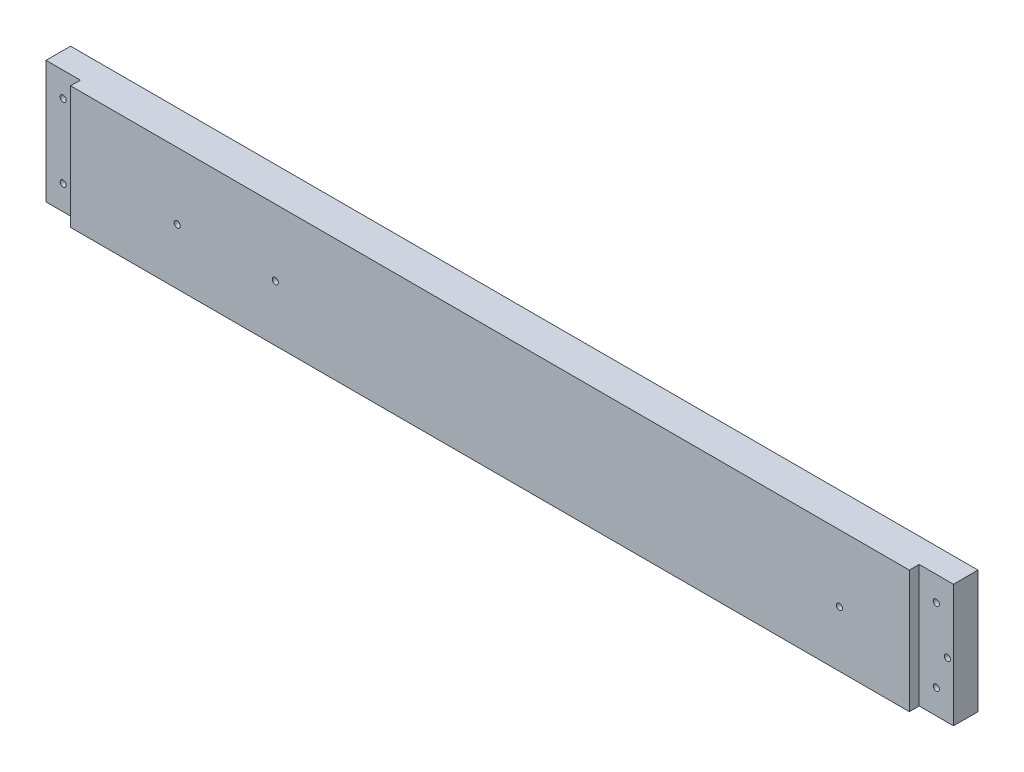
SolidWorks part; units mm, degrees
material "Pine"
ref_plane "Front Plane" through (0, 0, 0) normal (0, 0, 1) x (1, 0, 0)
ref_plane "Top Plane" through (0, 0, 0) normal (0, 1, 0) x (1, 0, 0)
ref_plane "Right Plane" through (0, 0, 0) normal (1, 0, 0) x (0, 0, -1)
sketch "Sketch1" plane through (0, 0, 0) normal (0, 0, 1) x (1, 0, 0)
  line L0 (8932.6508, -5243.5125) -> (10226.1458, -5243.5125)
  line L1 (9086.3208, -4722.0918) -> (10222.9708, -4853.7812)
  line L2 (8914.8708, -6342.0625) -> (10197.5708, -6342.0625)
  line L3 (8914.8708, -5808.6625) -> (10197.5708, -5808.6625)
  line L4 (8919.6333, -5253.0375) -> (10218.2083, -5253.0375)
  line L5 (9134.2633, -4656.1375) -> (9134.2633, -4638.3575)
  line L6 (9091.0833, -4638.3575) -> (9134.2633, -4638.3575)
  line L7 (9091.0833, -4567.2375) -> (9091.0833, -4638.3575)
  line L8 (9134.2633, -4656.1375) -> (9581.3033, -4656.1375)
  line L9 (9091.0833, -4567.2375) -> (9624.4833, -4567.2375)
  line L10 (9581.3033, -4656.1375) -> (9581.3033, -4638.3575)
  line L11 (9581.3033, -4638.3575) -> (9624.4833, -4638.3575)
  line L12 (9624.4833, -4567.2375) -> (9624.4833, -4638.3575)
  line L13 (8932.6508, -5225.7325) -> (9344.9775, -5225.7325)
  line L14 (8932.6508, -5256.2125) -> (8932.6508, -5243.5125)
  line L15 (8911.6958, -5256.2125) -> (8932.6508, -5256.2125)
  line L16 (8914.8708, -4722.0918) -> (9086.3208, -4722.0918)
  line L17 (8911.6958, -4715.5913) -> (8932.6508, -4715.5913)
  line L18 (8914.8708, -6342.0625) -> (8914.8708, -5808.6625)
  line L19 (12082.9917, -4722.0918) -> (10946.3417, -4853.7812)
  line L20 (12236.6617, -5243.5125) -> (10943.1667, -5243.5125)
  line L21 (10951.1042, -5253.0375) -> (12249.6792, -5253.0375)
  line L22 (10838.3917, -5656.2625) -> (11308.2917, -5656.2625)
  line L23 (10838.3917, -5719.7625) -> (11308.2917, -5719.7625)
  line L24 (10838.3917, -5742.5368) -> (11308.2917, -5742.5368)
  line L25 (10806.6417, -6342.0625) -> (11340.0417, -6342.0625)
  line L26 (10803.4667, -6335.7125) -> (11343.2167, -6335.7125)
  line L27 (10803.4667, -6317.9325) -> (11343.2167, -6317.9325)
  line L28 (10943.1667, -5225.7325) -> (11376.4483, -5225.7325)
  line L29 (11506.7292, -4754.5625) -> (10806.6417, -4827.5875)
  line L30 (11506.7292, -4567.2375) -> (11506.7292, -4754.5625)
  line L31 (10806.6417, -4567.2375) -> (10806.6417, -4827.5875)
  line L32 (10806.6417, -4567.2375) -> (11506.7292, -4567.2375)
  line L33 (10235.6708, -6329.3625) -> (10245.1958, -6329.3625)
  line L34 (10245.1958, -6329.3625) -> (10254.7208, -6278.5625)
  line L35 (10302.3458, -6329.3625) -> (10311.8708, -6278.5625)
  line L36 (10302.3458, -6329.3625) -> (10292.8208, -6329.3625)
  line L37 (10245.1958, -5821.3625) -> (10254.7208, -5872.1625)
  line L38 (10235.6708, -5821.3625) -> (10245.1958, -5821.3625)
  line L39 (10292.8208, -5821.3625) -> (10302.3458, -5821.3625)
  line L40 (10302.3458, -5821.3625) -> (10311.8708, -5872.1625)
  line L41 (10235.6708, -5821.3625) -> (10235.6708, -6329.3625)
  line L42 (10254.7208, -5872.1625) -> (10254.7208, -6278.5625)
  line L43 (10311.8708, -5872.1625) -> (10311.8708, -6278.5625)
  line L44 (10292.8208, -5821.3625) -> (10292.8208, -6329.3625)
  line L45 (8932.6508, -5225.7325) -> (8932.6508, -4715.5913)
  line L46 (8911.6958, -4715.5913) -> (8911.6958, -5256.2125)
  line L47 (8914.8708, -5248.275) -> (8914.8708, -4722.0918)
  line L48 (8919.6333, -5253.0375) -> (8914.8708, -5248.275)
  line L49 (8914.8708, -5145.0875) -> (8937.426, -5145.0875)
  line L50 (8914.8708, -5202.2375) -> (8937.426, -5202.2375)
  line L51 (10838.3917, -5656.2625) -> (10838.3917, -5719.7625)
  line L52 (10832.0417, -5736.1868) -> (10856.1717, -5736.1868)
  line L53 (10806.6417, -6342.0625) -> (10806.6417, -5818.7368)
  line L54 (10832.0417, -5649.9125) -> (10856.1717, -5649.9125)
  line L55 (10832.0417, -5726.1125) -> (10856.1717, -5726.1125)
  line L56 (10806.6417, -5818.7368) -> (10833.9015, -5818.7368)
  line L57 (10832.0417, -5806.0442) -> (10851.6815, -5806.0442)
  line L58 (10856.1717, -5801.5541) -> (10856.1717, -5736.1868)
  line L59 (10838.3917, -5814.2467) -> (10838.3917, -5742.5368)
  line L60 (10832.0417, -5806.0442) -> (10832.0417, -5736.1868)
  line L61 (10803.4667, -6317.9325) -> (10803.4667, -6335.7125)
  line L62 (10197.5708, -5808.6625) -> (10197.5708, -6342.0625)
  line L63 (9762.3842, -6348.4125) -> (9762.3842, -5802.3125)
  line L64 (9780.1642, -6348.4125) -> (9762.3842, -6348.4125)
  line L65 (9780.1642, -5802.3125) -> (9780.1642, -6348.4125)
  line L66 (9762.3842, -5802.3125) -> (9780.1642, -5802.3125)
  line L67 (9332.2775, -6348.4125) -> (9332.2775, -5802.3125)
  line L68 (9332.2775, -6348.4125) -> (9350.0575, -6348.4125)
  line L69 (9350.0575, -5802.3125) -> (9350.0575, -6348.4125)
  line L70 (9332.2775, -5802.3125) -> (9350.0575, -5802.3125)
  line L71 (9993.8374, -6061.075) -> (9993.8374, -6045.2418)
  line L72 (9998.5999, -6065.8375) -> (10014.4331, -6065.8375)
  line L73 (9998.5999, -6084.8875) -> (10014.4331, -6084.8875)
  line L74 (9993.8374, -6105.4832) -> (9993.8374, -6089.65)
  line L75 (9974.7874, -6105.4832) -> (9974.7874, -6089.65)
  line L76 (9954.1917, -6084.8875) -> (9970.0249, -6084.8875)
  line L77 (9974.7874, -6061.075) -> (9974.7874, -6045.2418)
  line L78 (9954.1917, -6065.8375) -> (9970.0249, -6065.8375)
  line L79 (10793.9417, -6237.2875) -> (10816.4969, -6237.2875)
  line L80 (10793.9417, -6294.4375) -> (10816.4969, -6294.4375)
  line L81 (10856.1717, -5649.9125) -> (10856.1717, -5726.1125)
  line L82 (10832.0417, -5726.1125) -> (10832.0417, -5649.9125)
  line L83 (10226.1458, -5225.7325) -> (10226.1458, -5243.5125)
  line L84 (10205.1908, -5257.8) -> (10205.1908, -4844.2499)
  line L85 (10230.9083, -4844.2499) -> (10230.9083, -5257.8)
  line L86 (10205.1908, -5257.8) -> (10230.9083, -5257.8)
  line L87 (10205.1908, -4844.2499) -> (10230.9083, -4844.2499)
  line L88 (10946.3417, -5176.8375) -> (10968.8969, -5176.8375)
  line L89 (9349.4676, -5141.9125) -> (9358.2674, -5141.9125)
  line L90 (10946.3417, -5119.6875) -> (10968.8969, -5119.6875)
  line L91 (9929.011, -4660.9635) -> (10066.0807, -4660.9635)
  line L92 (9929.011, -4678.7435) -> (10066.0807, -4678.7435)
  line L93 (10943.1667, -5225.7325) -> (10943.1667, -5243.5125)
  line L94 (10946.3417, -5248.275) -> (10951.1042, -5253.0375)
  line L95 (10946.3417, -5257.8063) -> (10946.3417, -4849.0188)
  line L96 (10964.1217, -5257.8) -> (10964.1217, -4844.2499)
  line L97 (10938.4042, -4844.2499) -> (10938.4042, -5257.8)
  line L98 (10938.4042, -5257.8) -> (10964.1217, -5257.8)
  line L99 (10964.1217, -4844.2499) -> (10938.4042, -4844.2499)
  line L100 (10344.8908, -4560.8875) -> (10369.0208, -4560.8875)
  line L101 (10344.8908, -4560.8875) -> (10369.0208, -4560.8875)
  line L102 (10800.2917, -4560.8875) -> (10824.4217, -4560.8875)
  line L103 (10200.4156, -5119.6875) -> (10222.9708, -5119.6875)
  line L104 (10200.4156, -5176.8375) -> (10222.9708, -5176.8375)
  line L105 (9344.9775, -5146.4026) -> (9344.9775, -5225.7325)
  line L106 (10344.8908, -4560.8875) -> (10344.8908, -4833.9375)
  line L107 (9792.8642, -5225.7325) -> (9792.8642, -5146.4026)
  line L108 (9362.7575, -5225.7325) -> (9775.0842, -5225.7325)
  line L109 (9680.3633, -4761.8396) -> (9680.3633, -4559.9604)
  line L110 (9656.2333, -4559.9604) -> (9680.3633, -4559.9604)
  line L111 (9656.2333, -4761.8396) -> (9680.3633, -4761.8396)
  line L112 (9656.2333, -4761.8396) -> (9656.2333, -4559.9604)
  line L113 (9779.5743, -5141.9125) -> (9788.374, -5141.9125)
  line L114 (10070.5708, -4665.4536) -> (10070.5708, -4674.2534)
  line L115 (9924.5208, -4674.2534) -> (9924.5208, -4665.4536)
  line L116 (12127.4417, -6188.3925) -> (12205.5015, -6188.3925)
  line L117 (12209.9917, -6170.6125) -> (12209.9917, -6183.9024)
  line L118 (9792.8642, -5225.7325) -> (10226.1458, -5225.7325)
  line L119 (9662.5833, -4754.5625) -> (10362.6708, -4827.5875)
  line L120 (9662.5833, -4567.2375) -> (9662.5833, -4754.5625)
  line L121 (10362.6708, -4567.2375) -> (10362.6708, -4827.5875)
  line L122 (9662.5833, -4567.2375) -> (10362.6708, -4567.2375)
  line L123 (10824.4217, -4833.9375) -> (10800.2917, -4833.9375)
  line L124 (10800.2917, -4833.9375) -> (10800.2917, -4560.8875)
  line L125 (10824.4217, -4560.8875) -> (10824.4217, -4833.9375)
  line L126 (10344.8908, -4833.9375) -> (10369.0208, -4833.9375)
  line L127 (10369.0208, -4833.9375) -> (10369.0208, -4560.8875)
  line L128 (10222.9708, -5248.275) -> (10218.2083, -5253.0375)
  line L129 (10222.9708, -5257.8063) -> (10222.9708, -4849.0188)
  line L130 (11734.6544, -5701.375) -> (11739.2301, -5701.375)
  line L131 (9362.7575, -5225.7325) -> (9362.7575, -5146.4026)
  line L132 (9775.0842, -5146.4026) -> (9775.0842, -5225.7325)
  line L133 (11761.3864, -5701.375) -> (11756.8282, -5701.375)
  line L134 (11734.6544, -5693.755) -> (11739.2301, -5693.755)
  line L135 (11761.4039, -5693.755) -> (11756.8282, -5693.755)
  line L136 (11734.6544, -5701.375) -> (11739.2301, -5701.375)
  line L137 (11744.3462, -5721.3024) -> (11744.3462, -5706.4179)
  line L138 (11751.7122, -5721.3024) -> (11751.7122, -5706.4179)
  line L139 (11740.0917, -6170.6125) -> (11740.0917, -6183.9024)
  line L140 (11689.2917, -6188.3925) -> (11822.6417, -6188.3925)
  line L141 (11689.2917, -6348.4093) -> (11689.2917, -6164.2657)
  line L142 (11689.2917, -6164.2657) -> (11746.4417, -6164.2657)
  line L143 (11746.4417, -6164.2657) -> (11746.4417, -6188.3925)
  line L144 (11689.2917, -6164.2657) -> (11746.4417, -6164.2657)
  line L145 (11340.0417, -5818.7368) -> (11340.0417, -6342.0625)
  line L146 (11290.5117, -5726.1125) -> (11314.6417, -5726.1125)
  line L147 (11290.5117, -5649.9125) -> (11290.5117, -5726.1125)
  line L148 (11340.0417, -5818.7368) -> (11312.7818, -5818.7368)
  line L149 (11314.6417, -5806.0442) -> (11295.0018, -5806.0442)
  line L150 (11290.5117, -5801.5541) -> (11290.5117, -5736.1868)
  line L151 (11308.2917, -5814.2467) -> (11308.2917, -5742.5368)
  line L152 (11314.6417, -5806.0442) -> (11314.6417, -5736.1868)
  line L153 (11290.5117, -5736.1868) -> (11314.6417, -5736.1868)
  line L154 (11848.0417, -6267.1325) -> (11962.3417, -6267.1325)
  line L155 (11962.3417, -6267.1325) -> (11962.3417, -6203.6325)
  line L156 (11343.2167, -6317.9325) -> (11343.2167, -6335.7125)
  line L157 (11365.4417, -5656.2625) -> (11365.4417, -5719.7625)
  line L158 (11365.4417, -5656.2625) -> (11479.7417, -5656.2625)
  line L159 (11778.1917, -6071.3937) -> (11802.3217, -6071.3937)
  line L160 (11314.6417, -5726.1125) -> (11314.6417, -5649.9125)
  line L161 (11314.6417, -5649.9125) -> (11290.5117, -5649.9125)
  line L162 (11308.2917, -5719.7625) -> (11308.2917, -5656.2625)
  line L163 (11689.2917, -6348.4093) -> (11713.4217, -6348.4093)
  line L164 (12203.6417, -6164.2657) -> (12260.7917, -6164.2657)
  line L165 (11713.4217, -6348.4093) -> (11713.4217, -6164.2657)
  line L166 (11695.6417, -6342.0625) -> (11695.6417, -6170.6125)
  line L167 (11695.6417, -6048.5337) -> (11699.4517, -6052.3437)
  line L168 (11822.6417, -6292.5325) -> (11822.6417, -6188.3925)
  line L169 (11695.6417, -6342.0625) -> (11695.6417, -6170.6125)
  line L170 (11848.0417, -6203.6325) -> (11962.3417, -6203.6325)
  line L171 (11848.0417, -6203.6325) -> (11848.0417, -6267.1325)
  line L172 (11987.7417, -6267.1325) -> (11987.7417, -6203.6325)
  line L173 (11784.5417, -6077.7437) -> (11784.5417, -6141.2438)
  line L174 (11517.8417, -5656.2625) -> (11632.1417, -5656.2625)
  line L175 (11632.1417, -5656.2625) -> (11632.1417, -5719.7625)
  line L176 (11632.1417, -5719.7625) -> (11517.8417, -5719.7625)
  line L177 (11517.8417, -5719.7625) -> (11517.8417, -5656.2625)
  line L178 (11692.4667, -6028.2137) -> (11692.4667, -6045.9937)
  line L179 (11695.6417, -5979.3188) -> (11718.1969, -5979.3188)
  line L180 (11695.6417, -5922.1687) -> (11718.1969, -5922.1687)
  line L181 (11821.0415, -5722.9375) -> (11821.0415, -5943.6)
  line L182 (11687.7042, -5651.5) -> (11701.9917, -5651.5)
  line L183 (11687.7042, -5651.5) -> (11687.7042, -6055.5251)
  line L184 (11687.7042, -6055.5251) -> (11701.9917, -6055.5251)
  line L185 (11701.9917, -6055.5251) -> (11701.9917, -5651.5)
  line L186 (11695.6417, -6055.2013) -> (11695.6417, -5649.595)
  line L187 (11695.6417, -5656.2625) -> (11695.6417, -6048.5337)
  line L188 (11695.6417, -6170.6125) -> (11740.0917, -6170.6125)
  line L189 (12203.6417, -6164.2657) -> (12203.6417, -6188.3925)
  line L190 (12254.4417, -6342.0625) -> (12254.4417, -6170.6125)
  line L191 (12129.0419, -5943.6) -> (12129.0419, -5722.9375)
  line L192 (12254.4417, -6048.5337) -> (12250.6317, -6052.3437)
  line L193 (12257.6167, -6045.9937) -> (12257.6167, -6028.2137)
  line L194 (12248.0917, -5651.5) -> (12262.3792, -5651.5)
  line L195 (12262.3792, -5651.5) -> (12262.3792, -6055.5251)
  line L196 (12262.3792, -6055.5251) -> (12248.0917, -6055.5251)
  line L197 (12248.0917, -6055.5251) -> (12248.0917, -5651.5)
  line L198 (12254.4417, -6141.2438) -> (12254.4417, -6077.7437)
  line L199 (12236.6617, -6164.2657) -> (12260.7917, -6164.2657)
  line L200 (12102.0417, -6267.1325) -> (11987.7417, -6267.1325)
  line L201 (11330.1865, -6237.2875) -> (11352.7417, -6237.2875)
  line L202 (11330.1865, -6294.4375) -> (11352.7417, -6294.4375)
  line L203 (11474.6617, -5851.8425) -> (11492.4417, -5851.8425)
  line L204 (11474.6617, -5808.6625) -> (11474.6617, -5851.8425)
  line L205 (11403.5417, -5808.6625) -> (11474.6617, -5808.6625)
  line L206 (11492.4417, -5851.8425) -> (11492.4417, -6298.8825)
  line L207 (11403.5417, -6342.0625) -> (11403.5417, -5808.6625)
  line L208 (11474.6617, -6298.8825) -> (11492.4417, -6298.8825)
  line L209 (11474.6617, -6342.0625) -> (11474.6617, -6298.8825)
  line L210 (11403.5417, -6342.0625) -> (11474.6617, -6342.0625)
  line L211 (11619.4417, -5851.8425) -> (11601.6617, -5851.8425)
  line L212 (11601.6617, -5808.6625) -> (11601.6617, -5851.8425)
  line L213 (11530.5417, -5808.6625) -> (11601.6617, -5808.6625)
  line L214 (11619.4417, -5851.8425) -> (11619.4417, -6298.8825)
  line L215 (11530.5417, -6342.0625) -> (11530.5417, -5808.6625)
  line L216 (11619.4417, -6298.8825) -> (11601.6617, -6298.8825)
  line L217 (11601.6617, -6342.0625) -> (11601.6617, -6298.8825)
  line L218 (11530.5417, -6342.0625) -> (11601.6617, -6342.0625)
  line L219 (11479.7417, -5719.7625) -> (11479.7417, -5656.2625)
  line L220 (11365.4417, -5719.7625) -> (11479.7417, -5719.7625)
  line L221 (11778.1917, -6147.5937) -> (11802.3217, -6147.5937)
  line L222 (11802.3217, -6071.3937) -> (11802.3217, -6147.5937)
  line L223 (11778.1917, -6147.5937) -> (11778.1917, -6071.3937)
  line L224 (12254.4417, -5922.1687) -> (12231.8865, -5922.1687)
  line L225 (12254.4417, -5979.3188) -> (12231.8865, -5979.3188)
  line L226 (12254.4417, -6055.2013) -> (12254.4417, -5649.595)
  line L227 (12254.4417, -6048.5337) -> (12254.4417, -5656.2625)
  line L228 (11841.6917, -5702.2873) -> (12108.3917, -5702.2873)
  line L229 (11822.6417, -6292.5325) -> (12127.4417, -6292.5325)
  line L230 (12127.4417, -6292.5325) -> (12127.4417, -6188.3925)
  line L231 (12254.4417, -6170.6125) -> (12209.9917, -6170.6125)
  line L232 (11695.6417, -6342.0625) -> (12254.4417, -6342.0625)
  line L233 (12236.6617, -6348.4093) -> (12260.7917, -6348.4093)
  line L234 (12260.7917, -6348.4093) -> (12260.7917, -6164.2657)
  line L235 (12236.6617, -6348.4093) -> (12236.6617, -6164.2657)
  line L236 (12102.0417, -6203.6325) -> (12102.0417, -6267.1325)
  line L237 (11987.7417, -6203.6325) -> (12102.0417, -6203.6325)
  line L238 (12236.6617, -6147.5937) -> (12236.6617, -6071.3937)
  line L239 (12203.6417, -6188.3925) -> (12260.7917, -6188.3925)
  line L240 (11098.7417, -4665.4536) -> (11098.7417, -4674.2534)
  line L241 (11394.2283, -5146.4026) -> (11394.2283, -5225.7325)
  line L242 (11376.4483, -5225.7325) -> (11376.4483, -5146.4026)
  line L243 (11394.2283, -5225.7325) -> (11806.555, -5225.7325)
  line L244 (11841.6917, -5964.2502) -> (12108.3917, -5964.2502)
  line L245 (12236.6617, -6147.5937) -> (12260.7917, -6147.5937)
  line L246 (12236.6617, -5256.2125) -> (12236.6617, -5243.5125)
  line L247 (12260.7917, -6147.5937) -> (12260.7917, -6071.3937)
  line L248 (12260.7917, -6071.3937) -> (12236.6617, -6071.3937)
  line L249 (12254.4417, -6077.7437) -> (11784.5417, -6077.7437)
  line L250 (11784.5417, -6141.2438) -> (12254.4417, -6141.2438)
  line L252 (12254.4417, -5656.2625) -> (11695.6417, -5656.2625)
  line L253 (11699.4517, -6052.3437) -> (12250.6317, -6052.3437)
  line L254 (11692.4667, -6045.9937) -> (12257.6167, -6045.9937)
  line L255 (11692.4667, -6028.2137) -> (12257.6167, -6028.2137)
  line L256 (11824.335, -5146.4026) -> (11824.335, -5225.7325)
  line L257 (11811.0451, -5141.9125) -> (11819.8449, -5141.9125)
  line L258 (11244.7917, -4674.2534) -> (11244.7917, -4665.4536)
  line L259 (11806.555, -5225.7325) -> (11806.555, -5146.4026)
  line L260 (11488.9492, -4761.8396) -> (11488.9492, -4559.9604)
  line L261 (11488.9492, -4559.9604) -> (11513.0792, -4559.9604)
  line L262 (11488.9492, -4761.8396) -> (11513.0792, -4761.8396)
  line L263 (11513.0792, -4761.8396) -> (11513.0792, -4559.9604)
  line L264 (11240.3015, -4660.9635) -> (11103.2318, -4660.9635)
  line L265 (11103.2318, -4678.7435) -> (11240.3015, -4678.7435)
  line L266 (12236.6617, -5225.7325) -> (12236.6617, -4715.5913)
  line L267 (12257.6167, -4715.5913) -> (12257.6167, -5256.2125)
  line L268 (12254.4417, -5248.275) -> (12254.4417, -4722.0918)
  line L269 (12236.6617, -5225.7325) -> (11824.335, -5225.7325)
  line L270 (12035.0492, -4656.1375) -> (12035.0492, -4638.3575)
  line L271 (12078.2292, -4638.3575) -> (12035.0492, -4638.3575)
  line L272 (12078.2292, -4567.2375) -> (12078.2292, -4638.3575)
  line L273 (12035.0492, -4656.1375) -> (11588.0092, -4656.1375)
  line L274 (11544.8292, -4567.2375) -> (12078.2292, -4567.2375)
  line L275 (11588.0092, -4656.1375) -> (11588.0092, -4638.3575)
  line L276 (11544.8292, -4638.3575) -> (11588.0092, -4638.3575)
  line L277 (11544.8292, -4567.2375) -> (11544.8292, -4638.3575)
  line L278 (12249.6792, -5253.0375) -> (12254.4417, -5248.275)
  line L280 (12257.6167, -5256.2125) -> (12236.6617, -5256.2125)
  line L281 (12231.8865, -5145.0875) -> (12254.4417, -5145.0875)
  line L282 (12231.8865, -5202.2375) -> (12254.4417, -5202.2375)
  line L283 (12236.6617, -4715.5913) -> (12257.6167, -4715.5913)
  line L284 (12082.9917, -4722.0918) -> (12254.4417, -4722.0918)
  line L285 (11380.9385, -5141.9125) -> (11389.7382, -5141.9125)
  circle A0 centre (8923.7608, -4778.9042) radius 1.5875
  circle A1 centre (9062.6598, -4736.3765) radius 2.3685
  circle A2 centre (9051.3958, -6281.7375) radius 22.225
  circle A3 centre (9083.1458, -6249.9875) radius 1.5875
  circle A4 centre (9083.1458, -6313.4875) radius 1.5875
  circle A5 centre (9019.6458, -6249.9875) radius 1.5875
  circle A6 centre (9019.6458, -6313.4875) radius 1.5875
  circle A7 centre (8972.3383, -5202.2375) radius 1.5875
  circle A8 centre (8923.7608, -5015.9708) radius 1.5875
  circle A9 centre (8923.7608, -5134.5042) radius 1.5875
  circle A10 centre (9054.5708, -5234.6225) radius 1.5875
  circle A11 centre (8923.7608, -4897.4375) radius 1.5875
  circle A12 centre (8972.3383, -5087.9375) radius 1.5875
  circle A13 centre (8972.3383, -5145.0875) radius 1.5875
  circle A14 centre (10847.2817, -5668.9625) radius 1.5875
  circle A15 centre (10847.2817, -5707.0625) radius 1.5875
  circle A16 centre (10847.2817, -5755.2368) radius 1.5875
  circle A17 centre (10851.4092, -6237.2875) radius 1.5875
  circle A18 centre (10851.4092, -6294.4375) radius 1.5875
  circle A19 centre (10847.2817, -5793.3442) radius 1.5875
  arc A20 (10833.9015, -5818.7368) -> (10838.3917, -5814.2467) centre (10836.1466, -5816.4918) ccw
  arc A21 (10851.6815, -5806.0442) -> (10856.1717, -5801.5541) centre (10853.9266, -5803.7992) ccw
  circle A22 centre (10882.8417, -6040.4375) radius 1.5875
  circle A23 centre (10882.8417, -6218.2375) radius 1.5875
  circle A24 centre (10882.8417, -5862.6375) radius 1.5875
  circle A25 centre (10908.2417, -6326.8225) radius 1.5875
  circle A26 centre (10908.2417, -6326.8225) radius 1.5875
  circle A27 centre (10851.4092, -6180.1375) radius 1.5875
  circle A28 centre (10815.5317, -4783.4231) radius 1.5875
  circle A29 centre (10815.5317, -4696.9488) radius 1.5875
  circle A30 centre (10815.5317, -4610.4746) radius 1.5875
  circle A31 centre (10979.1323, -4867.0082) radius 2.3685
  circle A32 centre (10190.1802, -4867.0082) radius 2.3685
  circle A33 centre (10955.2317, -4929.9812) radius 1.5875
  circle A34 centre (10955.2317, -5031.5812) radius 1.5875
  circle A35 centre (10214.0808, -4929.9812) radius 1.5875
  circle A36 centre (10214.0808, -5031.5812) radius 1.5875
  circle A37 centre (9341.1675, -6265.8625) radius 1.5875
  circle A38 centre (9771.2742, -5884.8625) radius 1.5875
  circle A39 centre (9771.2742, -6138.8625) radius 1.5875
  circle A40 centre (9771.2742, -6011.8625) radius 1.5875
  arc A41 (10036.2287, -6113.8083) -> (10051.3426, -6111.6033) centre (10042.9639, -6107.0732) ccw
  arc A42 (10051.3426, -6111.6033) -> (10051.3426, -6039.1217) centre (9984.3124, -6075.3625) ccw
  arc A43 (10051.3426, -6039.1217) -> (10036.2287, -6036.9167) centre (10042.9639, -6043.6518) ccw
  arc A44 (10034.5851, -6102.5431) -> (10034.5851, -6048.1819) centre (9984.3124, -6075.3625) ccw
  arc A45 (10034.5851, -6102.5431) -> (10036.2287, -6113.8083) centre (10042.9639, -6107.0732) ccw
  arc A46 (10036.2287, -6036.9167) -> (10034.5851, -6048.1819) centre (10042.9639, -6043.6518) ccw
  arc A47 (9945.8666, -6127.2787) -> (9948.0717, -6142.3927) centre (9952.6018, -6134.0139) ccw
  arc A48 (9948.0717, -6142.3927) -> (10020.5532, -6142.3927) centre (9984.3124, -6075.3625) ccw
  arc A49 (10020.5532, -6142.3927) -> (10022.7583, -6127.2787) centre (10016.0231, -6134.0139) ccw
  arc A50 (9957.1319, -6125.6352) -> (10011.493, -6125.6352) centre (9984.3124, -6075.3625) ccw
  arc A51 (9957.1319, -6125.6352) -> (9945.8666, -6127.2787) centre (9952.6018, -6134.0139) ccw
  arc A52 (10022.7583, -6127.2787) -> (10011.493, -6125.6352) centre (10016.0231, -6134.0139) ccw
  arc A53 (9932.3962, -6036.9167) -> (9917.2822, -6039.1217) centre (9925.661, -6043.6518) ccw
  arc A54 (9917.2822, -6039.1217) -> (9917.2822, -6111.6033) centre (9984.3124, -6075.3625) ccw
  arc A55 (9917.2822, -6111.6033) -> (9932.3962, -6113.8083) centre (9925.661, -6107.0732) ccw
  arc A56 (9934.0398, -6048.1819) -> (9934.0398, -6102.5431) centre (9984.3124, -6075.3625) ccw
  arc A57 (9934.0398, -6048.1819) -> (9932.3962, -6036.9167) centre (9925.661, -6043.6518) ccw
  arc A58 (9932.3962, -6113.8083) -> (9934.0398, -6102.5431) centre (9925.661, -6107.0732) ccw
  arc A59 (9945.8666, -6023.4463) -> (9957.1319, -6025.0898) centre (9952.6018, -6016.7111) ccw
  arc A60 (10011.493, -6025.0898) -> (10022.7583, -6023.4463) centre (10016.0231, -6016.7111) ccw
  arc A61 (10011.493, -6025.0898) -> (9957.1319, -6025.0898) centre (9984.3124, -6075.3625) ccw
  arc A62 (9948.0717, -6008.3323) -> (9945.8666, -6023.4463) centre (9952.6018, -6016.7111) ccw
  arc A63 (10020.5532, -6008.3323) -> (9948.0717, -6008.3323) centre (9984.3124, -6075.3625) ccw
  arc A64 (10022.7583, -6023.4463) -> (10020.5532, -6008.3323) centre (10016.0231, -6016.7111) ccw
  arc A65 (10005.0943, -6187.7574) -> (10096.7073, -6096.1443) centre (9984.3124, -6075.3625) ccw
  arc A66 (9993.8374, -6178.3911) -> (10005.0943, -6187.7574) centre (10003.3624, -6178.3911) ccw
  arc A67 (10001.6306, -6169.0249) -> (10077.9748, -6092.6807) centre (9984.3124, -6075.3625) ccw
  arc A68 (10087.3411, -6084.8875) -> (10077.9748, -6092.6807) centre (10087.3411, -6094.4125) ccw
  arc A69 (10001.6306, -6169.0249) -> (9993.8374, -6178.3911) centre (10003.3624, -6178.3911) ccw
  arc A70 (9963.5306, -6187.7574) -> (9974.7874, -6178.3911) centre (9965.2624, -6178.3911) ccw
  arc A71 (9871.9176, -6096.1443) -> (9963.5306, -6187.7574) centre (9984.3124, -6075.3625) ccw
  arc A72 (9881.2838, -6084.8875) -> (9871.9176, -6096.1443) centre (9881.2838, -6094.4125) ccw
  arc A73 (9890.65, -6092.6807) -> (9966.9943, -6169.0249) centre (9984.3124, -6075.3625) ccw
  arc A74 (9974.7874, -6178.3911) -> (9966.9943, -6169.0249) centre (9965.2624, -6178.3911) ccw
  arc A75 (9890.65, -6092.6807) -> (9881.2838, -6084.8875) centre (9881.2838, -6094.4125) ccw
  arc A76 (9871.9176, -6054.5807) -> (9881.2838, -6065.8375) centre (9881.2838, -6056.3125) ccw
  arc A77 (9963.5306, -5962.9676) -> (9871.9176, -6054.5807) centre (9984.3124, -6075.3625) ccw
  arc A78 (9974.7874, -5972.3339) -> (9963.5306, -5962.9676) centre (9965.2624, -5972.3339) ccw
  arc A79 (9966.9943, -5981.7001) -> (9890.65, -6058.0443) centre (9984.3124, -6075.3625) ccw
  arc A80 (9881.2838, -6065.8375) -> (9890.65, -6058.0443) centre (9881.2838, -6056.3125) ccw
  arc A81 (9966.9943, -5981.7001) -> (9974.7874, -5972.3339) centre (9965.2624, -5972.3339) ccw
  arc A82 (10077.9748, -6058.0443) -> (10087.3411, -6065.8375) centre (10087.3411, -6056.3125) ccw
  arc A83 (9993.8374, -5972.3339) -> (10001.6306, -5981.7001) centre (10003.3624, -5972.3339) ccw
  arc A84 (10077.9748, -6058.0443) -> (10001.6306, -5981.7001) centre (9984.3124, -6075.3625) ccw
  arc A85 (10087.3411, -6065.8375) -> (10096.7073, -6054.5807) centre (10087.3411, -6056.3125) ccw
  arc A86 (10096.7073, -6054.5807) -> (10005.0943, -5962.9676) centre (9984.3124, -6075.3625) ccw
  arc A87 (10005.0943, -5962.9676) -> (9993.8374, -5972.3339) centre (10003.3624, -5972.3339) ccw
  arc A88 (10014.4331, -6065.8375) -> (10018.7361, -6059.0339) centre (10014.4331, -6061.075) ccw
  arc A89 (10018.7361, -6059.0339) -> (10000.641, -6040.9388) centre (9984.3124, -6075.3625) ccw
  arc A90 (10000.641, -6040.9388) -> (9993.8374, -6045.2418) centre (9998.5999, -6045.2418) ccw
  arc A91 (9993.8374, -6061.075) -> (9998.5999, -6065.8375) centre (9998.5999, -6061.075) ccw
  arc A92 (9993.8374, -6105.4832) -> (10000.641, -6109.7862) centre (9998.5999, -6105.4832) ccw
  arc A93 (10000.641, -6109.7862) -> (10018.7361, -6091.6911) centre (9984.3124, -6075.3625) ccw
  arc A94 (10018.7361, -6091.6911) -> (10014.4331, -6084.8875) centre (10014.4331, -6089.65) ccw
  arc A95 (9998.5999, -6084.8875) -> (9993.8374, -6089.65) centre (9998.5999, -6089.65) ccw
  arc A96 (9954.1917, -6084.8875) -> (9949.8888, -6091.6911) centre (9954.1917, -6089.65) ccw
  arc A97 (9949.8888, -6091.6911) -> (9967.9839, -6109.7862) centre (9984.3124, -6075.3625) ccw
  arc A98 (9967.9839, -6109.7862) -> (9974.7874, -6105.4832) centre (9970.0249, -6105.4832) ccw
  arc A99 (9974.7874, -6089.65) -> (9970.0249, -6084.8875) centre (9970.0249, -6089.65) ccw
  arc A100 (9970.0249, -6065.8375) -> (9974.7874, -6061.075) centre (9970.0249, -6061.075) ccw
  arc A101 (9949.8888, -6059.0339) -> (9954.1917, -6065.8375) centre (9954.1917, -6061.075) ccw
  arc A102 (9967.9839, -6040.9388) -> (9949.8888, -6059.0339) centre (9984.3124, -6075.3625) ccw
  arc A103 (9974.7874, -6045.2418) -> (9967.9839, -6040.9388) centre (9970.0249, -6045.2418) ccw
  arc A104 (10096.7073, -6096.1443) -> (10087.3411, -6084.8875) centre (10087.3411, -6094.4125) ccw
  circle A105 centre (9771.2742, -6265.8625) radius 1.5875
  circle A106 centre (9341.1675, -5884.8625) radius 1.5875
  circle A107 centre (9341.1675, -6138.8625) radius 1.5875
  circle A108 centre (9341.1675, -6011.8625) radius 1.5875
  circle A109 centre (11037.2315, -4887.5494) radius 15.0812
  arc A110 (9349.4676, -5141.9125) -> (9344.9775, -5146.4026) centre (9347.2226, -5144.1576) ccw
  arc A111 (9362.7575, -5146.4026) -> (9358.2674, -5141.9125) centre (9360.5124, -5144.1576) ccw
  circle A112 centre (9946.7458, -4669.8535) radius 1.5875
  arc A113 (9924.5208, -4674.2534) -> (9929.011, -4678.7435) centre (9926.7659, -4676.4984) ccw
  circle A114 centre (11003.8092, -5176.8375) radius 1.5875
  circle A115 centre (11003.8092, -5119.6875) radius 1.5875
  circle A116 centre (10353.7808, -4696.9488) radius 1.5875
  circle A117 centre (10353.7808, -4610.4746) radius 1.5875
  circle A118 centre (10353.7808, -4783.4231) radius 1.5875
  circle A119 centre (11003.8092, -5062.5375) radius 1.5875
  circle A120 centre (9353.8675, -5160.9625) radius 1.5875
  circle A121 centre (9638.7708, -5234.6225) radius 1.5875
  circle A122 centre (9671.4733, -4724.1144) radius 1.5875
  circle A123 centre (9671.4733, -4661.3637) radius 1.5875
  circle A124 centre (9671.4733, -4598.6129) radius 1.5875
  arc A125 (9792.8642, -5146.4026) -> (9788.374, -5141.9125) centre (9790.6191, -5144.1576) ccw
  arc A126 (9779.5743, -5141.9125) -> (9775.0842, -5146.4026) centre (9777.3292, -5144.1576) ccw
  circle A127 centre (10048.3458, -4669.8535) radius 1.5875
  arc A128 (10070.5708, -4665.4536) -> (10066.0807, -4660.9635) centre (10068.3258, -4663.2086) ccw
  arc A129 (10066.0807, -4678.7435) -> (10070.5708, -4674.2534) centre (10068.3258, -4676.4984) ccw
  circle A130 centre (9997.5458, -4669.8535) radius 1.5875
  arc A131 (9929.011, -4660.9635) -> (9924.5208, -4665.4536) centre (9926.7659, -4663.2086) ccw
  circle A132 centre (10132.081, -4887.5494) radius 15.0812
  circle A133 centre (10165.5033, -5176.8375) radius 1.5875
  circle A134 centre (10165.5033, -5119.6875) radius 1.5875
  circle A135 centre (9486.3708, -5234.6225) radius 1.5875
  circle A136 centre (10165.5033, -5062.5375) radius 1.5875
  circle A137 centre (9206.9708, -5234.6225) radius 1.5875
  circle A138 centre (10070.5708, -5234.6225) radius 1.5875
  circle A139 centre (9918.1708, -5234.6225) radius 1.5875
  circle A140 centre (9783.9742, -5160.9625) radius 1.5875
  circle A141 centre (9783.9742, -5193.9825) radius 1.5875
  circle A142 centre (9353.8675, -5193.9825) radius 1.5875
  circle A143 centre (11073.3417, -6326.8225) radius 1.5875
  circle A144 centre (11073.3417, -6326.8225) radius 1.5875
  circle A145 centre (11295.2742, -6180.1375) radius 1.5875
  circle A146 centre (11295.2742, -6294.4375) radius 1.5875
  circle A147 centre (11295.2742, -6237.2875) radius 1.5875
  circle A148 centre (11975.0417, -5692.775) radius 3.4925
  circle A149 centre (11263.8417, -5862.6375) radius 1.5875
  arc A150 (11739.2301, -5701.375) -> (11744.3462, -5706.4179) centre (11748.0292, -5697.565) ccw
  arc A151 (11751.7122, -5706.4179) -> (11756.8282, -5701.375) centre (11748.0292, -5697.565) ccw
  arc A152 (11744.3462, -5721.3024) -> (11751.7122, -5721.3024) centre (11748.0292, -5725.505) ccw
  arc A153 (11734.6544, -5693.755) -> (11724.9787, -5697.565) centre (11730.5667, -5697.565) ccw
  arc A154 (11756.8282, -5693.755) -> (11739.2301, -5693.755) centre (11748.0292, -5697.565) ccw
  arc A155 (11724.9787, -5697.565) -> (11734.6544, -5701.375) centre (11730.5667, -5697.565) ccw
  arc A156 (11761.3864, -5701.375) -> (11771.0797, -5697.565) centre (11765.4842, -5697.565) ccw
  arc A157 (11771.0797, -5697.565) -> (11761.4039, -5693.755) centre (11765.4917, -5697.565) ccw
  arc A158 (11740.0917, -6183.9024) -> (11744.5818, -6188.3925) centre (11742.3367, -6186.1474) ccw
  arc A159 (12205.5015, -6188.3925) -> (12209.9917, -6183.9024) centre (12207.7466, -6186.1474) ccw
  circle A160 centre (11299.4017, -5793.3442) radius 1.5875
  arc A161 (11308.2917, -5814.2467) -> (11312.7818, -5818.7368) centre (11310.5367, -5816.4918) ccw
  arc A162 (11290.5117, -5801.5541) -> (11295.0018, -5806.0442) centre (11292.7567, -5803.7992) ccw
  circle A163 centre (11704.5317, -6314.149) radius 1.5875
  circle A164 centre (11748.9817, -6208.7125) radius 1.5875
  circle A165 centre (11263.8417, -6218.2375) radius 1.5875
  circle A166 centre (11263.8417, -6040.4375) radius 1.5875
  circle A167 centre (11238.4417, -6326.8225) radius 1.5875
  circle A168 centre (11238.4417, -6326.8225) radius 1.5875
  circle A169 centre (11299.4017, -5668.9625) radius 1.5875
  circle A170 centre (11299.4017, -5707.0625) radius 1.5875
  circle A171 centre (11726.7567, -6179.5025) radius 1.5875
  circle A172 centre (11704.5317, -6199.3198) radius 1.5875
  circle A173 centre (11748.9817, -6272.2125) radius 1.5875
  circle A174 centre (11704.5317, -6256.7344) radius 1.5875
  circle A175 centre (11299.4017, -5755.2368) radius 1.5875
  circle A176 centre (11913.4467, -6301.4225) radius 1.5875
  circle A177 centre (11790.2567, -6301.4225) radius 1.5875
  circle A178 centre (11793.4317, -6128.5437) radius 1.5875
  circle A179 centre (11753.1092, -5865.0188) radius 1.5875
  circle A180 centre (11809.9417, -6037.1038) radius 1.5875
  circle A181 centre (11809.9417, -6037.1038) radius 1.5875
  circle A182 centre (11753.1092, -5922.1687) radius 1.5875
  circle A183 centre (11975.0417, -5973.7625) radius 3.4925
  circle A184 centre (11975.0417, -6037.1038) radius 1.5875
  circle A185 centre (11753.1092, -5979.3188) radius 1.5875
  circle A186 centre (11975.0417, -6037.1038) radius 1.5875
  arc A187 (11841.6917, -5702.2873) -> (11821.0415, -5722.9375) centre (11841.6917, -5722.9375) ccw
  circle A188 centre (11811.5292, -5833.2687) radius 3.4925
  arc A189 (11821.0415, -5943.6) -> (11841.6917, -5964.2502) centre (11841.6917, -5943.6) ccw
  circle A190 centre (12196.9742, -5865.0188) radius 1.5875
  arc A191 (12129.0419, -5722.9375) -> (12108.3917, -5702.2873) centre (12108.3917, -5722.9375) ccw
  circle A192 centre (12036.6367, -6301.4225) radius 1.5875
  circle A193 centre (12159.8267, -6301.4225) radius 1.5875
  circle A194 centre (12138.5542, -5833.2687) radius 3.4925
  circle A195 centre (12197.2917, -5761.0375) radius 15.0812
  circle A196 centre (11793.4317, -6090.4437) radius 1.5875
  circle A197 centre (12196.9742, -5922.1687) radius 1.5875
  arc A198 (12108.3917, -5964.2502) -> (12129.0419, -5943.6) centre (12108.3917, -5943.6) ccw
  circle A199 centre (12196.9742, -5979.3188) radius 1.5875
  circle A200 centre (12201.1017, -6272.2125) radius 1.5875
  circle A201 centre (12245.5517, -6314.149) radius 1.5875
  circle A202 centre (12245.5517, -6256.7344) radius 1.5875
  circle A203 centre (12201.1017, -6208.7125) radius 1.5875
  circle A204 centre (12223.3267, -6179.5025) radius 1.5875
  circle A205 centre (12245.5517, -6199.3198) radius 1.5875
  circle A206 centre (11171.7667, -4669.8535) radius 1.5875
  circle A207 centre (11222.5667, -4669.8535) radius 1.5875
  arc A208 (11240.3015, -4678.7435) -> (11244.7917, -4674.2534) centre (11242.5466, -4676.4984) ccw
  circle A209 centre (11385.3383, -5193.9825) radius 1.5875
  circle A210 centre (12106.6527, -4736.3765) radius 2.3685
  circle A211 centre (12140.1417, -6037.1038) radius 1.5875
  circle A212 centre (12140.1417, -6037.1038) radius 1.5875
  circle A213 centre (12245.5517, -6090.4437) radius 1.5875
  circle A214 centre (12245.5517, -6128.5437) radius 1.5875
  circle A215 centre (11385.3383, -5160.9625) radius 1.5875
  arc A216 (11824.335, -5146.4026) -> (11819.8449, -5141.9125) centre (11822.0899, -5144.1576) ccw
  arc A217 (11811.0451, -5141.9125) -> (11806.555, -5146.4026) centre (11808.8001, -5144.1576) ccw
  circle A218 centre (11815.445, -5193.9825) radius 1.5875
  circle A219 centre (11815.445, -5160.9625) radius 1.5875
  circle A220 centre (11530.5417, -5234.6225) radius 1.5875
  circle A221 centre (11962.3417, -5234.6225) radius 1.5875
  arc A222 (11244.7917, -4665.4536) -> (11240.3015, -4660.9635) centre (11242.5466, -4663.2086) ccw
  circle A223 centre (11682.9417, -5234.6225) radius 1.5875
  circle A224 centre (11497.8392, -4724.1144) radius 1.5875
  circle A225 centre (11497.8392, -4661.3637) radius 1.5875
  circle A226 centre (11497.8392, -4598.6129) radius 1.5875
  circle A227 centre (11120.9667, -4669.8535) radius 1.5875
  arc A228 (11103.2318, -4660.9635) -> (11098.7417, -4665.4536) centre (11100.9867, -4663.2086) ccw
  arc A229 (11098.7417, -4674.2534) -> (11103.2318, -4678.7435) centre (11100.9867, -4676.4984) ccw
  circle A230 centre (12196.9742, -5202.2375) radius 1.5875
  circle A231 centre (12245.5517, -5015.9708) radius 1.5875
  circle A232 centre (12245.5517, -5134.5042) radius 1.5875
  circle A233 centre (12114.7417, -5234.6225) radius 1.5875
  circle A234 centre (12245.5517, -4897.4375) radius 1.5875
  circle A235 centre (12245.5517, -4778.9042) radius 1.5875
  circle A236 centre (12196.9742, -5087.9375) radius 1.5875
  circle A237 centre (12196.9742, -5145.0875) radius 1.5875
  circle A238 centre (11098.7417, -5234.6225) radius 1.5875
  circle A239 centre (11251.1417, -5234.6225) radius 1.5875
  arc A240 (11380.9385, -5141.9125) -> (11376.4483, -5146.4026) centre (11378.6934, -5144.1576) ccw
  arc A241 (11394.2283, -5146.4026) -> (11389.7382, -5141.9125) centre (11391.9833, -5144.1576) ccw
sketch "Sketch2" plane through (0, 0, 0) normal (0, 0, 1) x (1, 0, 0)
  line L0 (11308.2917, -5719.7625) -> (11308.2917, -5656.2625)
  line L1 (11308.2917, -5656.2625) -> (10838.3917, -5656.2625)
  line L2 (10838.3917, -5656.2625) -> (10838.3917, -5719.7625)
  line L3 (10838.3917, -5719.7625) -> (11308.2917, -5719.7625)
extrude "Extrude1" add sketch "Sketch2" against normal blind 17.78
sketch "Sketch3" plane through (0, 0, 0) normal (0, 0, 1) x (1, 0, 0)
  line L0 (11290.5117, -5656.2625) -> (11308.2917, -5656.2625)
  line L1 (11308.2917, -5656.2625) -> (11308.2917, -5719.7625)
  line L2 (11308.2917, -5719.7625) -> (11290.5117, -5719.7625)
  line L3 (11290.5117, -5719.7625) -> (11290.5117, -5656.2625)
  line L4 (10856.1717, -5656.2625) -> (10856.1717, -5719.7625)
  line L5 (10856.1717, -5719.7625) -> (10838.3917, -5719.7625)
  line L6 (10838.3917, -5719.7625) -> (10838.3917, -5656.2625)
  line L7 (10838.3917, -5656.2625) -> (10856.1717, -5656.2625)
  line L8 (10838.3917, -5719.7625) -> (11308.2917, -5719.7625) construction
  line L9 (11308.2917, -5656.2625) -> (10838.3917, -5656.2625) construction
  dimension "D1" = 17.78
  dimension "D2" = 17.78
extrude "Cut-Extrude1" cut sketch "Sketch3" against normal blind 5.08
sketch "Sketch4" plane through (0, 0, 0) normal (0, 0, 1) x (1, 0, 0)
  circle A0 centre (10847.2817, -5668.9625) radius 1.5875
  circle A1 centre (10847.2817, -5707.0625) radius 1.5875
  circle A2 centre (11299.4017, -5707.0625) radius 1.5875
  circle A3 centre (11299.4017, -5668.9625) radius 1.5875
extrude "Cut-Extrude2" cut sketch "Sketch4" against normal up to surface (17.78 mm away) up to face at (11073.3417, -5688.0125, -17.78)
sketch "Sketch5" plane through (0, 0, -17.78) normal (0, 0, -1) x (-1, 0, 0)
  circle A0 centre (-10911.4167, -5690.7874) radius 1.5875
  circle A1 centre (-10962.2167, -5690.7874) radius 1.5875
  circle A2 centre (-11254.3167, -5690.7874) radius 1.5875
  circle A3 centre (-11305.1167, -5690.7874) radius 1.5875
extrude "Cut-Extrude3" cut sketch "Sketch5" against normal up to surface (17.78 mm away) up to face at (11073.3417, -5688.0125, 0)
